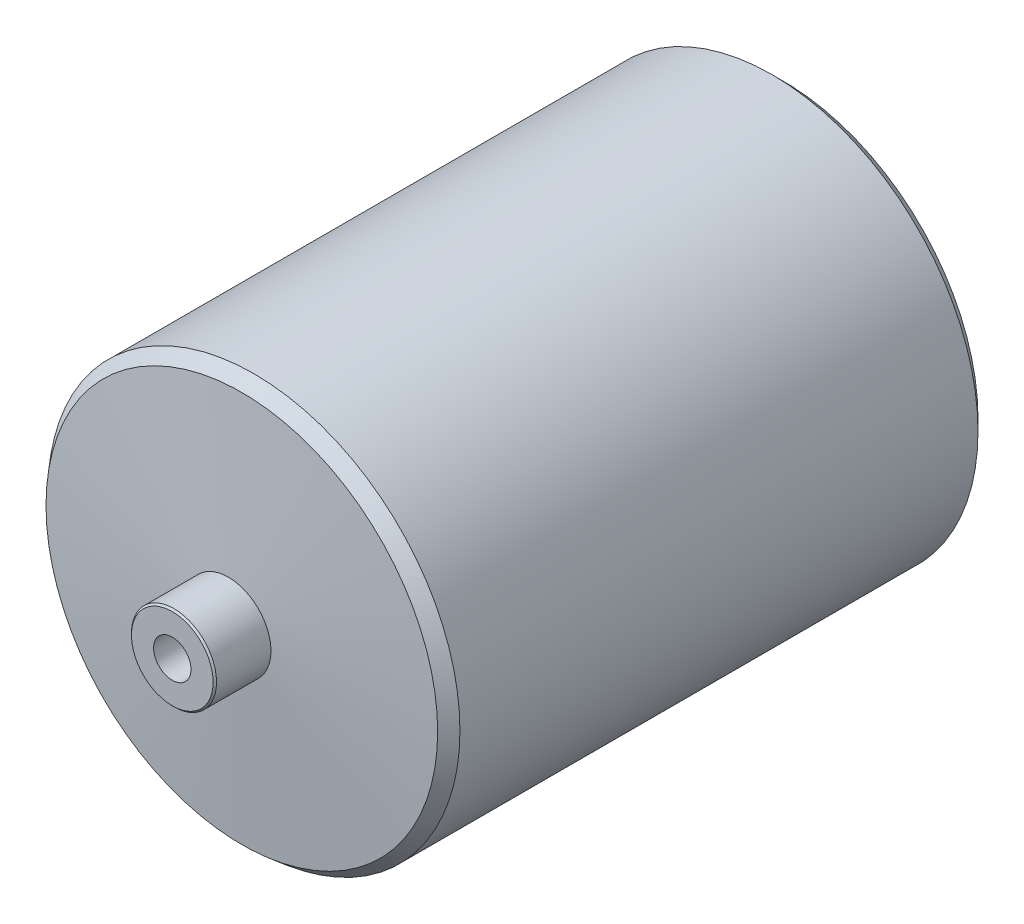
SolidWorks part; units mm, degrees
ref_plane "Alzado" through (0, 0, 0) normal (0, 0, 1) x (1, 0, 0)
ref_plane "Planta" through (0, 0, 0) normal (0, 1, 0) x (1, 0, 0)
ref_plane "Vista lateral" through (0, 0, 0) normal (1, 0, 0) x (0, 0, -1)
sketch "Croquis1" plane through (0, 0, 0) normal (1, 0, 0) x (0, 0, -1)
  line L0 (0, 0) -> (0, 12.5)
  line L4 (20.7044, 60.5562) -> (179.2956, 60.5562)
  line L7 (183.5, 12.5) -> (200, 12.5)
  line L8 (200, 12.5) -> (200, 0)
  line L9 (200, 0) -> (0, 0)
  line L10 (0, 12.5) -> (16.5, 12.5)
  line L11 (16.5, 12.5) -> (20.7044, 60.5562)
  line L12 (183.5, 12.5) -> (179.2956, 60.5562)
  dimension "D1" = 200
  dimension "D2" = 12.5
  dimension "D3" = 12.5
  dimension "D4" = 16.5
  dimension "D5" = 60.5562
  dimension "D6" = 85
  dimension "D7" = 85
  dimension "D8" = 16.5
revolve "Revolución1" add sketch "Croquis1" angle 360 about L9
chamfer "Chaflán1" distance 3 angle 45 2 edges at (-60.5562, 0, -179.2956) (-60.5562, 0, -20.7044)
chamfer "Chaflán2" distance 0.5 angle 45 2 edges at (-12.5, 0, -200) (-12.5, 0, 0)
sketch "Croquis2" plane through (0, 0, 0) normal (0, 0, 1) x (1, 0, 0)
  circle A0 centre (0, 0) radius 5
  dimension "D1" = 10
sketch "Croquis3" plane through (0, 0, -200) normal (0, 0, -1) x (-1, 0, 0)
  circle A0 centre (0, 0) radius 5
  dimension "D1" = 10
hole_wizard "Taladro de margen para M101" positions "Croquis4" profile "Croquis5" hole size "M10" standard "DIN"
sketch "Croquis4" plane through (0, 0, -200) normal (0, 0, -1) x (-1, 0, 0)
  point P0 (0, 0)
sketch "Croquis5" plane through (0, 0, -200) normal (1, 0, 0) x (0, 1, 0)
  line L0 (0, 0) -> (0, 59)
  line L1 (0, 59) -> (5.5, 55.6953)
  line L2 (5.5, 55.6953) -> (5.5, 0)
  line L5 (5.5, 0) -> (0, 0)
  line L10 (0, 59) -> (-5.5, 55.6953) construction
  line L11 (0, -6.35) -> (0, 107.95) construction
  dimension "Diámetro de taladro" = 11
  dimension "Profundidad de taladro" = 59
  dimension "Ángulo de perforador" = 118
hole_wizard "Taladro de margen para M102" positions "Croquis6" profile "Croquis7" hole size "M10" standard "GB"
sketch "Croquis6" plane through (0, 0, 0) normal (0, 0, 1) x (1, 0, 0)
  point P0 (0, 0)
sketch "Croquis7" plane through (0, 0, 0) normal (1, 0, 0) x (0, -1, 0)
  line L0 (0, 0) -> (0, 59)
  line L1 (0, 59) -> (5.5, 55.6953)
  line L2 (5.5, 55.6953) -> (5.5, 0)
  line L5 (5.5, 0) -> (0, 0)
  line L10 (0, 59) -> (-5.5, 55.6953) construction
  line L11 (0, -6.35) -> (0, 107.95) construction
  dimension "Diámetro de taladro" = 11
  dimension "Profundidad de taladro" = 59
  dimension "Ángulo de perforador" = 118
